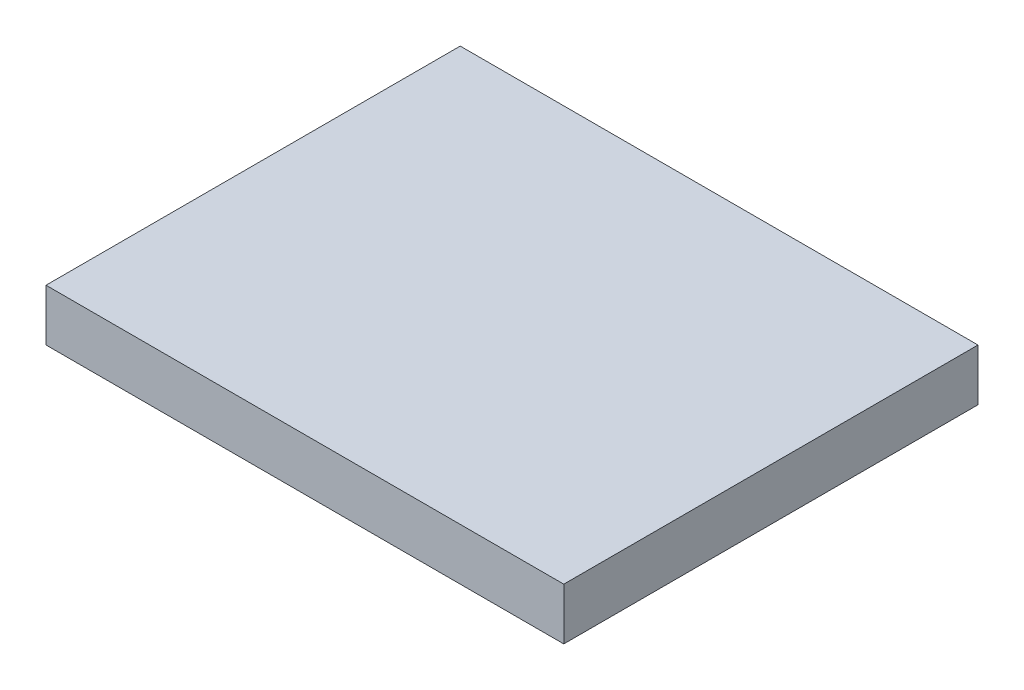
SolidWorks part; units mm, degrees
ref_plane "Piano frontale" through (0, 0, 0) normal (0, 0, 1) x (1, 0, 0)
ref_plane "Piano superiore" through (0, 0, 0) normal (0, 1, 0) x (1, 0, 0)
ref_plane "Piano destro" through (0, 0, 0) normal (1, 0, 0) x (0, 0, -1)
sketch "Schizzo1" plane through (0, 0, 0) normal (0, 1, 0) x (1, 0, 0)
  line L1 (0, 0) -> (100, 0)
  line L2 (0, 0) -> (0, -80)
  line L3 (0, -80) -> (100, -80)
  line L4 (100, 0) -> (100, -80)
  dimension "D1" = 80
  dimension "D2" = 100
extrude "Estrusione-Estrusione1" add sketch "Schizzo1" along normal blind 10
